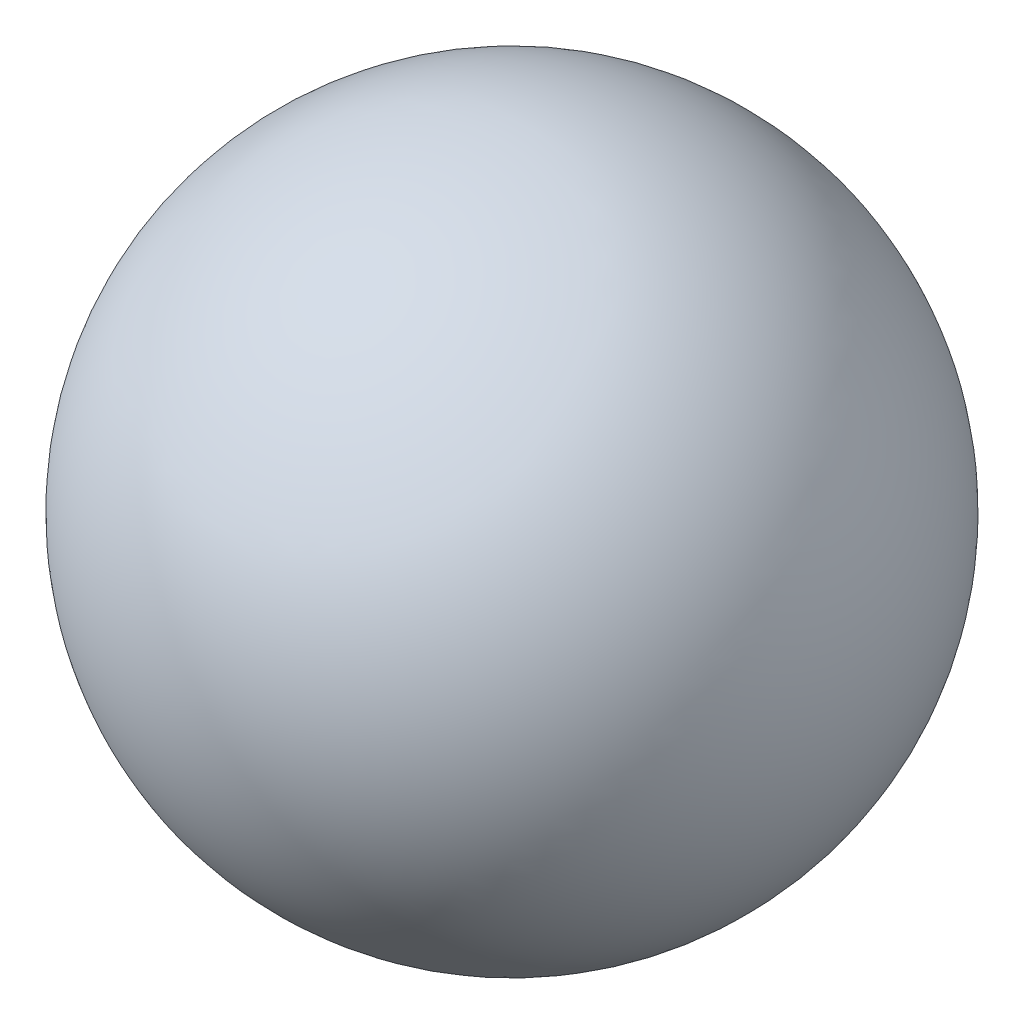
SolidWorks part; units mm, degrees
ref_plane "Front" through (0, 0, 0) normal (0, 0, 1) x (1, 0, 0)
ref_plane "Top" through (0, 0, 0) normal (0, 1, 0) x (1, 0, 0)
ref_plane "Right" through (0, 0, 0) normal (1, 0, 0) x (0, 0, -1)
sketch "Sketch1" plane through (0, 0, 0) normal (0, 1, 0) x (1, 0, 0)
  line L0 (0, 1.8) -> (0, -1.8)
  arc A0 (0, 1.8) -> (0, -1.8) centre (0, 0) ccw
revolve "Revolve1" add sketch "Sketch1" angle 360 about L0
